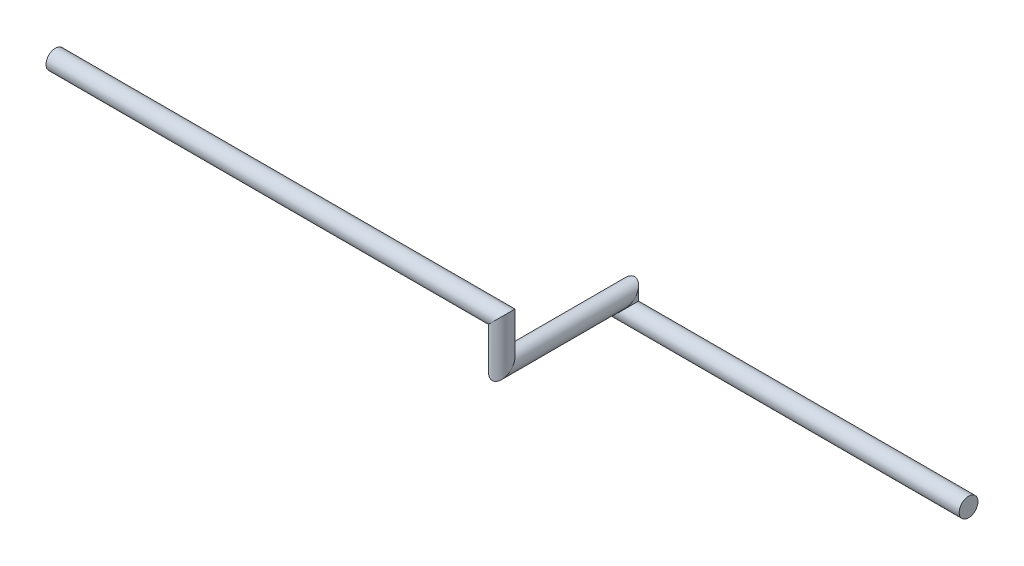
SolidWorks part; units mm, degrees
ref_plane "Alzado" through (0, 0, 0) normal (0, 0, 1) x (1, 0, 0)
ref_plane "Planta" through (0, 0, 0) normal (0, 1, 0) x (1, 0, 0)
ref_plane "Vista lateral" through (0, 0, 0) normal (1, 0, 0) x (0, 0, -1)
sketch3d "Croquis3D1"
  line L0 (0, 0, 0) -> (-500, 0, 0)
  line L1 (-500, 0, 0) -> (-500, 20, 0)
  line L2 (-500, 20, 0) -> (-500, 20, 180)
  line L3 (-500, 20, 180) -> (-500, 80, 180)
  line L4 (-500, 80, 180) -> (-1150, 80, 180)
  dimension "D1" = 500
  dimension "D2" = 20
  dimension "D3" = 180
  dimension "D4" = 60
  dimension "D5" = 650
sketch "Croquis1" plane through (0, 0, 0) normal (1, 0, 0) x (0, 0, -1)
  circle A0 centre (0, 0) radius 13.7
  dimension "D1" = 27.4
sweep "Barrer1" add profiles "Croquis1" path "Croquis3D1"
